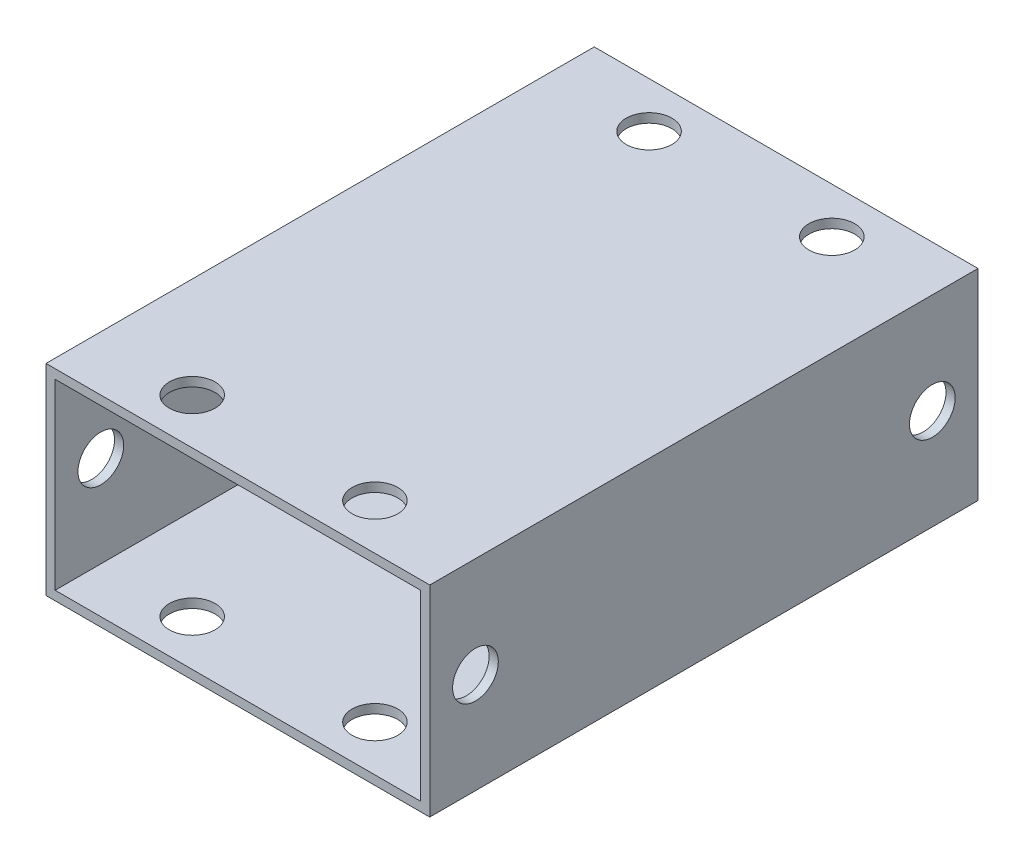
SolidWorks part; units mm, degrees
ref_plane "Front Plane" through (0, 0, 0) normal (0, 0, 1) x (1, 0, 0)
ref_plane "Top Plane" through (0, 0, 0) normal (0, 1, 0) x (1, 0, 0)
ref_plane "Right Plane" through (0, 0, 0) normal (1, 0, 0) x (0, 0, -1)
sketch "Sketch1" plane through (0, 0, 0) normal (0, 0, 1) x (1, 0, 0)
  line L0 (-20, -10) -> (20, -10) construction
  line L1 (-20, -10) -> (20, -10) construction
  line L2 (-20, -10) -> (-20, 10)
  line L3 (-20, 10) -> (20, 10)
  line L4 (20, -10) -> (20, 10)
  line L5 (-20, -10) -> (20, 10) construction
  line L6 (-20, 10) -> (20, -10) construction
  line L7 (-21, -10) -> (-20, -10)
  line L8 (-21, -10) -> (-21, 11)
  line L9 (-21, 11) -> (21, 11)
  line L10 (21, -10) -> (21, 11)
  line L11 (-21, -10) -> (21, 11) construction
  line L12 (-21, 11) -> (21, -10) construction
  line L13 (20, -10) -> (21, -10)
  point P0 (0, 0)
  point P6 (0, 0.5)
  dimension "D1" = 1
  dimension "D2" = 1
  dimension "D3" = 40
  dimension "D4" = 20
extrude "Boss-Extrude1" add sketch "Sketch1" along normal blind 60
sketch "Sketch2" plane through (0, 10, 0) normal (0, -1, 0) x (1, 0, 0)
  line L1 (-20, 60) -> (-20, 0) construction
  line L3 (-20, 0) -> (20, 0) construction
  line L4 (0, 30) -> (0, 0) construction
  line L5 (20, 60) -> (20, 0) construction
  line L6 (-20, 30) -> (20, 30) construction
  line L7 (-20, 5) -> (0, 5) construction
  circle A3 centre (-10, 5) radius 2.5
  circle A4 centre (10, 5) radius 2.5
  circle A5 centre (10, 55) radius 2.5
  circle A6 centre (-10, 55) radius 2.5
  dimension "D2" = 5
  dimension "D3" = 5
extrude "Cut-Extrude1" cut sketch "Sketch2" against normal through all
sketch "Sketch3" plane through (20, 0, 0) normal (-1, 0, 0) x (0, 0, 1)
  line L0 (5, 10) -> (5, -10) construction
  line L1 (60, 10) -> (0, 10) construction
  line L2 (60, -10) -> (0, -10) construction
  line L3 (30, 10) -> (30, -10) construction
  line L4 (0, 10) -> (0, -10) construction
  circle A0 centre (5, 0) radius 2.5
  circle A1 centre (55, 0) radius 2.5
  dimension "D1" = 5
  dimension "D2" = 5
extrude "Cut-Extrude2" cut sketch "Sketch3" against normal through all both and the other way through all
sketch "Sketch4" plane through (0, -10, 0) normal (0, -1, 0) x (1, 0, 0)
  line L1 (21, 60) -> (-21, 60)
  line L2 (21, 60) -> (21, 0)
  line L3 (21, 0) -> (-21, 0)
  line L20 (-21, 60) -> (-21, 0)
  circle A1 centre (-10, 5) radius 2.5
  circle A2 centre (-10, 5) radius 2.5
  circle A3 centre (-10, 55) radius 2.5
  circle A4 centre (-10, 55) radius 2.5
  circle A5 centre (10, 55) radius 2.5
  circle A6 centre (10, 55) radius 2.5
  circle A7 centre (10, 5) radius 2.5
  circle A8 centre (10, 5) radius 2.5
  dimension "D1" = 0
  dimension "D2" = 0
  dimension "D3" = 0
  dimension "D4" = 0
extrude "Boss-Extrude2" add sketch "Sketch4" along normal blind 1
